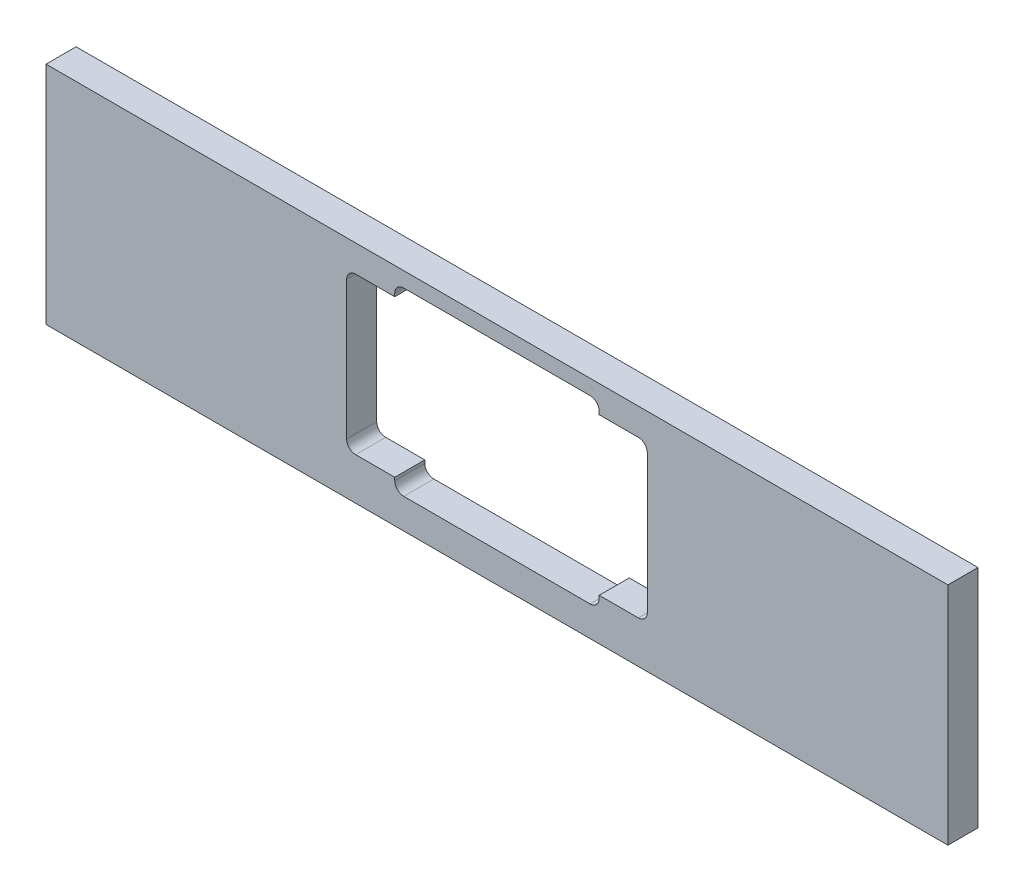
SolidWorks part; units mm, degrees
ref_plane "Ebene vorne" through (0, 0, 0) normal (0, 0, 1) x (1, 0, 0)
ref_plane "Ebene oben" through (0, 0, 0) normal (0, 1, 0) x (1, 0, 0)
ref_plane "Ebene rechts" through (0, 0, 0) normal (1, 0, 0) x (0, 0, -1)
sketch "Skizze1" plane through (0, 0, 0) normal (0, 0, 1) x (1, 0, 0)
  line L0 (-150, -75) -> (-150, 55) construction
  line L1 (150, -150) -> (-150, -150)
  line L2 (150, -150) -> (150, -75)
  line L3 (150, -75) -> (-150, -75)
  line L4 (-150, -150) -> (-150, -75)
  dimension "D1" = 75
extrude "Linear austragen1" add sketch "Skizze1" along normal blind 10
sketch "Skizze2" plane through (0, 0, 10) normal (0, 0, 1) x (1, 0, 0)
  line L1 (-117, -140) -> (47, -140) construction
  line L2 (-34, -140) -> (34, -140)
  line L3 (-50, -140) -> (-34, -140) construction
  line L4 (-50, -140) -> (-50, -136) construction
  line L5 (50, -140) -> (150, -140) construction
  line L6 (-50, -136) -> (-34, -136)
  line L7 (-50, -140) -> (-150, -140) construction
  line L8 (-150, 55) -> (-150, -150) construction
  line L9 (150, -150) -> (150, -75) construction
  line L10 (-34, -140) -> (-34, -136)
  line L11 (50, -140) -> (34, -140) construction
  line L12 (50, -140) -> (50, -136) construction
  line L13 (50, -136) -> (34, -136)
  line L14 (34, -140) -> (34, -136)
  line L15 (-50, -136) -> (-50, -84)
  line L16 (-34, -80) -> (34, -80)
  line L17 (-50, -84) -> (-34, -84)
  line L18 (-50, -84) -> (-50, -80) construction
  line L19 (-50, -80) -> (-34, -80) construction
  line L20 (-34, -84) -> (-34, -80)
  line L21 (50, -80) -> (34, -80) construction
  line L22 (50, -80) -> (50, -84) construction
  line L23 (50, -84) -> (34, -84)
  line L24 (34, -80) -> (34, -84)
  line L25 (50, -84) -> (50, -136)
  line L27 (-50, -83) -> (-50, -137) construction
  line L28 (47, -80) -> (-117, -80) construction
  point P30 (-34, -126.4454)
  dimension "D1" = 68
  dimension "D2" = 52
extrude "Schnitt-Linear austragen1" cut sketch "Skizze2" against normal blind 10
fillet "Verrundung1" radius 3 8 edges at (-50, -136, 5) (-34, -140, 5) (50, -136, 5) (34, -140, 5) (50, -84, 5) (34, -80, 5) (-50, -84, 5) (-34, -80, 5)
